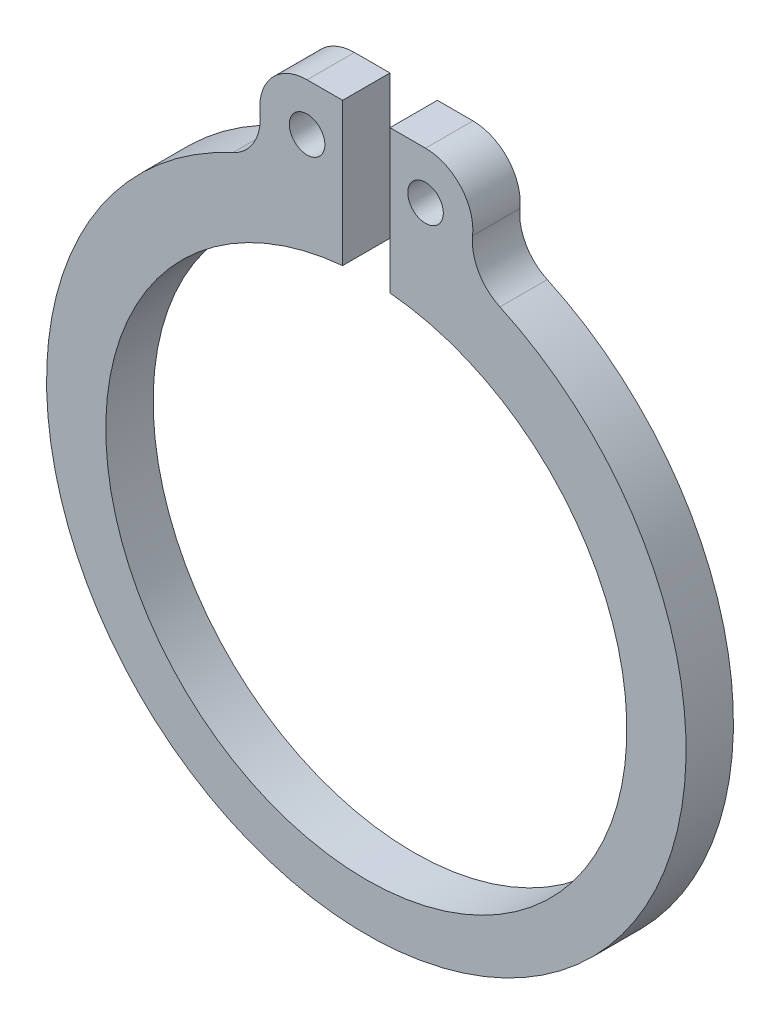
SolidWorks part; units mm, degrees
material "Gri Dökme Demir"
ref_plane "Ön Düzlem" through (0, 0, 0) normal (0, 0, 1) x (1, 0, 0)
ref_plane "Üst Düzlem" through (0, 0, 0) normal (0, 1, 0) x (1, 0, 0)
ref_plane "Sağ Düzlem" through (0, 0, 0) normal (1, 0, 0) x (0, 0, -1)
sketch "Çizim1" plane through (0, 0, 0) normal (0, 0, 1) x (1, 0, 0)
  line L0 (0, 0) -> (0, -0.5) construction
  line L1 (0, 0) -> (0, 13.5) construction
  line L2 (0, 0) -> (0, 16) construction
  line L3 (0, 16) -> (-2.5, 16) construction
  line L4 (-2.5, 16) -> (-2.5, 14.5) construction
  line L5 (-2.5, 16.4989) -> (-1, 16.4989)
  line L6 (-1, 16.4989) -> (-1, 10.4545)
  line L7 (2.5, 16.4989) -> (1, 16.4989)
  line L8 (1, 16.4989) -> (1, 10.4545)
  line L9 (-1, 21.4654) -> (-1, 6.4917) construction
  arc A0 (-5.6412, 12.2649) -> (5.6412, 12.2649) centre (0, 0) ccw
  arc A2 (-1, 10.4545) -> (1, 10.4545) centre (0, -0.5) ccw
  circle A3 centre (-2.5, 14.5) radius 0.75
  arc A4 (-4.4879, 14.291) -> (-2.5, 16.4989) centre (-2.5, 14.5) cw
  arc A5 (-4.4879, 14.291) -> (-5.6412, 12.2649) centre (-6.477, 14.0819) cw
  circle A6 centre (2.5, 14.5) radius 0.75
  arc A7 (4.4879, 14.291) -> (5.6412, 12.2649) centre (6.477, 14.0819) ccw
  arc A8 (4.4879, 14.291) -> (2.5, 16.4989) centre (2.5, 14.5) ccw
  dimension "D1" = 0.5
  dimension "D2" = 27
  dimension "D3" = 22
  dimension "D7" = 1.5
  dimension "D9" = 1.9989
  dimension "D8" = 1.5
  dimension "D10" = 2
  dimension "D4" = 1
  dimension "D5" = 16
  dimension "D6" = 2.5
extrude "Yükseklik-Ekstrüzyon1" add sketch "Çizim1" along normal mid plane 2
